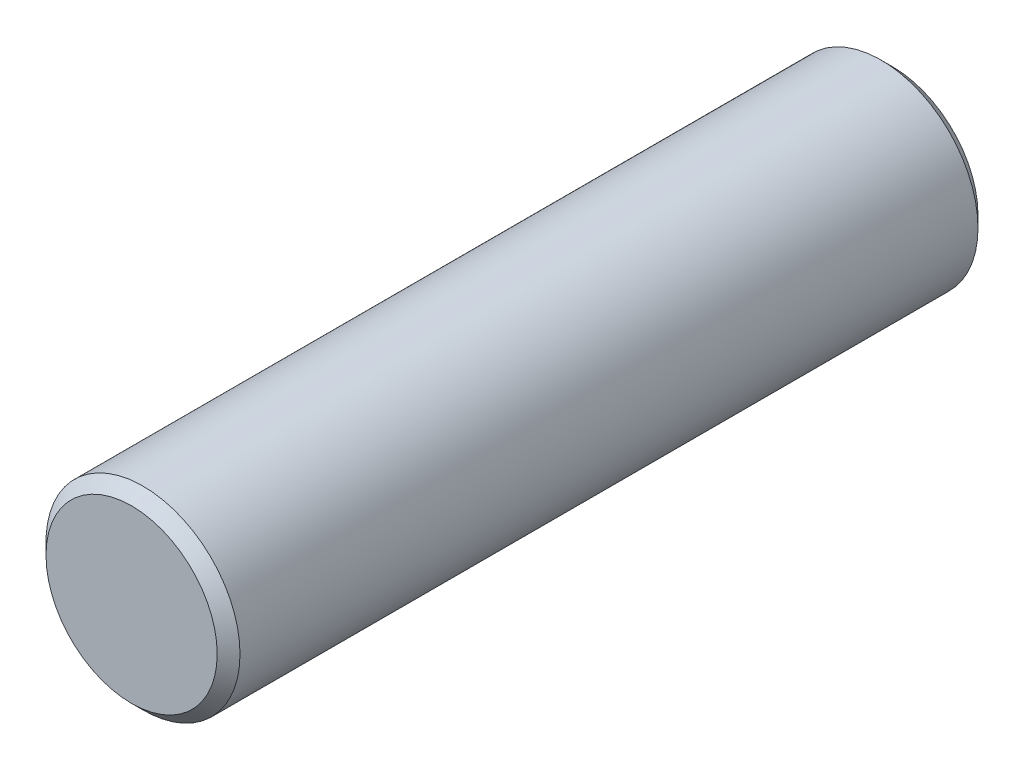
SolidWorks part; units mm, degrees
ref_plane "Front Plane" through (0, 0, 0) normal (0, 0, 1) x (1, 0, 0)
ref_plane "Top Plane" through (0, 0, 0) normal (0, 1, 0) x (1, 0, 0)
ref_plane "Right Plane" through (0, 0, 0) normal (1, 0, 0) x (0, 0, -1)
sketch "Sketch1" plane through (0, 0, 0) normal (0, 0, 1) x (1, 0, 0)
  circle A0 centre (0, 0) radius 3.2385
  dimension "D1" = 6.477
extrude "Boss-Extrude1" add sketch "Sketch1" along normal blind 25.4
chamfer "Chamfer1" distance 0.381 angle 45 2 edges at (3.2385, 0, 0) (3.2385, 0, 25.4)
